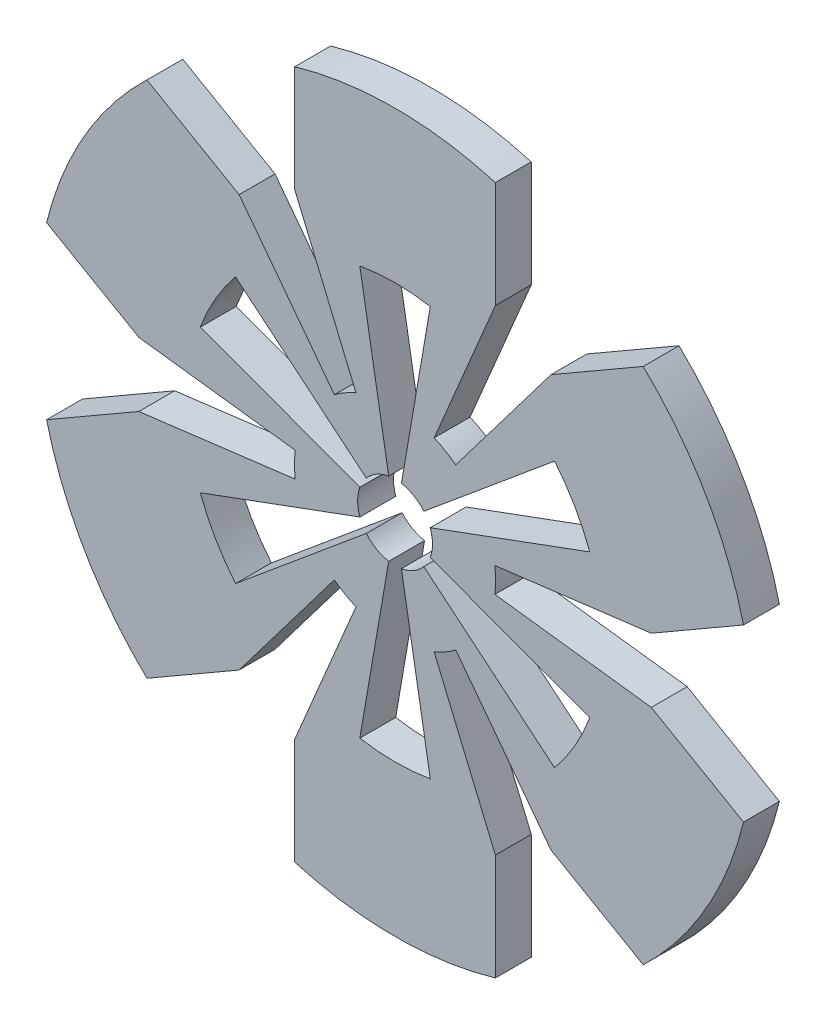
SolidWorks part; units mm, degrees
ref_plane "Front Plane" through (0, 0, 0) normal (0, 0, 1) x (1, 0, 0)
ref_plane "Top Plane" through (0, 0, 0) normal (0, 1, 0) x (1, 0, 0)
ref_plane "Right Plane" through (0, 0, 0) normal (1, 0, 0) x (0, 0, -1)
sketch "Sketch1" plane through (0, 0, 0) normal (0, 0, 1) x (1, 0, 0)
  line L0 (0, 0) -> (61.8183, 0) construction
  line L1 (1.651, 2.8596) -> (25.2758, 43.779) construction
  line L2 (5.0811, 4.2297) -> (2.5467, 2.1199)
  line L3 (1.1224, 6.5152) -> (0.5625, 3.2654)
  line L4 (6.2036, 2.2856) -> (3.1092, 1.1455)
  line L5 (0, 0) -> (0, 78.2171) construction
  line L6 (6.2036, -2.2856) -> (3.1092, -1.1455)
  line L7 (-5.0811, 4.2297) -> (-2.5467, 2.1199)
  line L8 (-1.1224, 6.5152) -> (-0.5625, 3.2654)
  line L9 (-6.2036, 2.2856) -> (-3.1092, 1.1455)
  line L10 (-6.2036, -2.2856) -> (-3.1092, -1.1455)
  line L11 (-5.0811, -4.2297) -> (-2.5467, -2.1199)
  line L12 (-1.1224, -6.5152) -> (-0.5625, -3.2654)
  line L13 (1.1224, -6.5152) -> (0.5625, -3.2654)
  line L14 (5.0811, -4.2297) -> (2.5467, -2.1199)
  line L15 (22.6794, 2.8416) -> (30.8387, 7.5524)
  line L16 (13.8006, 18.2201) -> (21.9599, 22.9309)
  line L17 (13.8006, -18.2201) -> (21.9599, -22.9309)
  line L18 (22.6794, -2.8416) -> (30.8387, -7.5524)
  line L19 (-8.8788, -21.0617) -> (-8.8788, -30.4833)
  line L20 (8.8788, -21.0617) -> (8.8788, -30.4833)
  line L21 (-22.6794, -2.8416) -> (-30.8387, -7.5524)
  line L22 (-13.8006, -18.2201) -> (-21.9599, -22.9309)
  line L23 (-13.8006, 18.2201) -> (-21.9599, 22.9309)
  line L24 (-22.6794, 2.8416) -> (-30.8387, 7.5524)
  line L27 (0, 0) -> (34.0353, 19.6503) construction
  line L28 (5.0811, 4.2297) -> (14.1156, 11.7501)
  line L29 (6.2036, 2.2856) -> (17.2336, 6.3494)
  line L30 (5.0811, -4.2297) -> (14.1156, -11.7501)
  line L31 (6.2036, -2.2856) -> (17.2336, -6.3494)
  line L32 (-1.1224, -6.5152) -> (-3.1181, -18.0995)
  line L33 (1.1224, -6.5152) -> (3.1181, -18.0995)
  line L34 (-6.2036, -2.2856) -> (-17.2336, -6.3494)
  line L35 (-5.0811, -4.2297) -> (-14.1156, -11.7501)
  line L36 (-5.0811, 4.2297) -> (-14.1156, 11.7501)
  line L37 (-6.2036, 2.2856) -> (-17.2336, 6.3494)
  line L38 (1.1224, 6.5152) -> (3.1181, 18.0995)
  line L39 (-1.1224, 6.5152) -> (-3.1181, 18.0995)
  line L40 (8.8788, 21.0617) -> (8.8788, 30.4833)
  line L41 (-8.8788, 21.0617) -> (-8.8788, 30.4833)
  line L54 (-8.8788, 30.4833) -> (-8.8788, 21.0617) construction
  arc A0 (-8.8788, 21.0617) -> (-13.8006, 18.2201) centre (0, 0) ccw construction
  arc A1 (0.5625, 3.2654) -> (2.5467, 2.1199) centre (0, 0) cw
  arc A2 (8.8788, 30.4833) -> (-8.8788, 30.4833) centre (0, 0) ccw
  arc A3 (30.8387, 7.5524) -> (21.9599, 22.9309) centre (0, 0) ccw
  arc A4 (21.9599, -22.9309) -> (30.8387, -7.5524) centre (0, 0) ccw
  circle A5 centre (0, 0) radius 18.3661 construction
  arc A6 (-8.8788, -30.4833) -> (8.8788, -30.4833) centre (0, 0) ccw
  arc A7 (-2.5467, 2.1199) -> (-0.5625, 3.2654) centre (0, 0) cw
  arc A8 (-3.1092, 1.1455) -> (-3.1092, -1.1455) centre (0, 0) ccw
  arc A9 (-2.5467, -2.1199) -> (-0.5625, -3.2654) centre (0, 0) ccw
  circle A10 centre (0, 0) radius 3.3135 construction
  arc A11 (0.5625, -3.2654) -> (2.5467, -2.1199) centre (0, 0) ccw
  arc A12 (-30.8387, -7.5524) -> (-21.9599, -22.9309) centre (0, 0) ccw
  arc A13 (3.1092, 1.1455) -> (3.1092, -1.1455) centre (0, 0) cw
  arc A14 (-21.9599, 22.9309) -> (-30.8387, 7.5524) centre (0, 0) ccw
  arc A16 (8.8788, 21.0617) -> (13.8006, 18.2201) centre (0, 0) cw
  arc A18 (22.6794, 2.8416) -> (22.6794, -2.8416) centre (0, 0) cw
  arc A20 (13.8006, -18.2201) -> (8.8788, -21.0617) centre (0, 0) cw
  arc A22 (-8.8788, -21.0617) -> (-13.8006, -18.2201) centre (0, 0) cw
  arc A23 (-22.6794, -2.8416) -> (-22.6794, 2.8416) centre (0, 0) cw
  arc A31 (14.1156, 11.7501) -> (17.2336, 6.3494) centre (0, 0) cw
  circle A32 centre (0, 0) radius 6.6112 construction
  arc A35 (17.2336, -6.3494) -> (14.1156, -11.7501) centre (0, 0) cw
  arc A37 (3.1181, -18.0995) -> (-3.1181, -18.0995) centre (0, 0) cw
  arc A39 (-14.1156, -11.7501) -> (-17.2336, -6.3494) centre (0, 0) cw
  arc A41 (-17.2336, 6.3494) -> (-14.1156, 11.7501) centre (0, 0) cw
  arc A43 (-3.1181, 18.0995) -> (3.1181, 18.0995) centre (0, 0) cw
  arc A44 (-13.8006, 18.2201) -> (-8.8788, 21.0617) centre (0, 0) cw
  circle A45 centre (0, 0) radius 9.1026 construction
  arc A47 (-6.2036, 2.2856) -> (-5.0811, 4.2297) centre (0, 0) cw [skipped]
  arc A48 (-1.1224, 6.5152) -> (0, 6.6112) centre (0, 0) cw [skipped]
  arc A49 (5.7255, 3.3056) -> (6.2036, 2.2856) centre (0, 0) cw [skipped]
  arc A50 (6.2036, -2.2856) -> (5.0811, -4.2297) centre (0, 0) cw [skipped]
  arc A51 (1.1224, -6.5152) -> (-1.1224, -6.5152) centre (0, 0) cw [skipped]
  arc A52 (-5.0811, -4.2297) -> (-6.2036, -2.2856) centre (0, 0) cw [skipped]
  dimension "D1" = 30
  dimension "D3" = 30
extrude "Extrude1" add sketch "Sketch1" along normal blind 3.175
sketch "Sketch2" plane through (0, 0, 3.175) normal (0, 0, 1) x (1, 0, 0)
  line L0 (0, 0) -> (0, 69.4182) construction
  line L1 (0, 0) -> (75, 0) construction
  line L2 (0, 0) -> (28.8123, 49.9043) construction
  line L3 (8.8788, 21.0617) -> (3.4582, 8.2032)
  line L4 (13.8006, 18.2201) -> (5.3751, 7.0965)
  line L5 (22.6794, 2.8416) -> (8.8333, 1.1068)
  line L6 (22.6794, -2.8416) -> (8.8333, -1.1068)
  line L7 (13.8006, -18.2201) -> (5.3751, -7.0965)
  line L8 (8.8788, -21.0617) -> (3.4582, -8.2032)
  line L9 (-8.8788, -21.0617) -> (-3.4582, -8.2032)
  line L10 (-13.8006, -18.2201) -> (-5.3751, -7.0965)
  line L11 (-22.6794, -2.8416) -> (-8.8333, -1.1068)
  line L12 (-22.6794, 2.8416) -> (-8.8333, 1.1068)
  line L13 (-13.8006, 18.2201) -> (-5.3751, 7.0965)
  line L14 (-8.8788, 21.0617) -> (-3.4582, 8.2032)
  arc A0 (8.8788, 21.0617) -> (13.8006, 18.2201) centre (0, 0) cw
  circle A1 centre (0, 0) radius 8.9024 construction
  arc A2 (3.4582, 8.2032) -> (5.3751, 7.0965) centre (0, 0) cw
  arc A3 (22.6794, 2.8416) -> (22.6794, -2.8416) centre (0, 0) cw
  arc A4 (8.8333, 1.1068) -> (8.8333, -1.1068) centre (0, 0) cw
  arc A5 (13.8006, -18.2201) -> (8.8788, -21.0617) centre (0, 0) cw
  arc A6 (5.3751, -7.0965) -> (3.4582, -8.2032) centre (0, 0) cw
  arc A7 (-8.8788, -21.0617) -> (-13.8006, -18.2201) centre (0, 0) cw
  arc A8 (-3.4582, -8.2032) -> (-5.3751, -7.0965) centre (0, 0) cw
  arc A9 (-22.6794, -2.8416) -> (-22.6794, 2.8416) centre (0, 0) cw
  arc A10 (-8.8333, -1.1068) -> (-8.8333, 1.1068) centre (0, 0) cw
  arc A11 (-13.8006, 18.2201) -> (-8.8788, 21.0617) centre (0, 0) cw
  arc A12 (-5.3751, 7.0965) -> (-3.4582, 8.2032) centre (0, 0) cw
  dimension "D1" = 30
extrude "Cut-Extrude1" cut sketch "Sketch2" against normal through all
